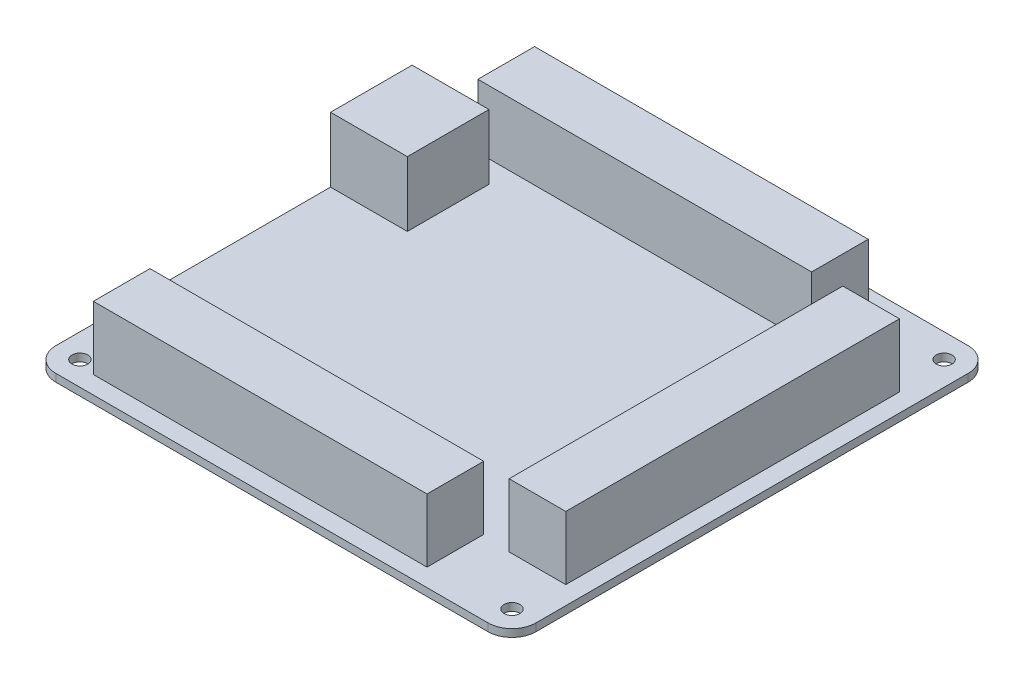
SolidWorks part; units mm, degrees
ref_plane "Front" through (0, 0, 0) normal (0, 0, 1) x (1, 0, 0)
ref_plane "Top" through (0, 0, 0) normal (0, 1, 0) x (1, 0, 0)
ref_plane "Right" through (0, 0, 0) normal (1, 0, 0) x (0, 0, -1)
sketch "Sketch1" plane through (0, 0, 0) normal (0, 1, 0) x (1, 0, 0)
  line L1 (-50, -50) -> (50, -50)
  line L2 (-50, -50) -> (-50, 50)
  line L3 (-50, 50) -> (50, 50)
  line L4 (50, -50) -> (50, 50)
  line L5 (-50, -50) -> (50, 50) construction
  line L6 (-50, 50) -> (50, -50) construction
  point P0 (0, 0)
  dimension "D1" = 100
  dimension "D2" = 100
extrude "Boss-Extrude1" add sketch "Sketch1" along normal blind 1.6
fillet "Fillet1" radius 5 4 edges at (-50, 0.8, -50) (50, 0.8, -50) (50, 0.8, 50) (-50, 0.8, 50)
hole_wizard "Ø3.3 (3.3) Diameter Hole1" positions "Sketch3" profile "Sketch2" hole size "Ø3.3" standard "ANSI Metric" end condition through all
sketch "Sketch3" plane through (0, 1.6, 0) normal (0, 1, 0) x (1, 0, 0)
  line L0 (-45, -50) -> (45, -50) construction
  line L1 (-50, 45) -> (-50, -45) construction
  line L2 (50, -45) -> (50, 45) construction
  line L3 (45, 50) -> (-45, 50) construction
  point P0 (45, -45)
  point P2 (-45, -45)
  point P4 (-45, 45)
  point P6 (45, 45)
  dimension "D1" = 5
  dimension "D2" = 5
  dimension "D3" = 5
  dimension "D4" = 5
sketch "Sketch2" plane through (45, 1.6, 45) normal (1, 0, 0) x (0, 0, 1)
  line L0 (0, 0) -> (0, 1.6)
  line L1 (0, 1.6) -> (1.65, 1.6)
  line L2 (1.65, 1.6) -> (1.65, 0)
  line L5 (1.65, 0) -> (0, 0)
  line L11 (0, -6.35) -> (0, 107.95) construction
  dimension "Thru Hole Dia." = 3.3
  dimension "Thru Hole Depth" = 1.6
sketch "Sketch4" plane through (0, 1.6, 0) normal (0, 1, 0) x (1, 0, 0)
  line L0 (-50, 29.2) -> (-34, 29.2)
  line L1 (-50, 45) -> (-50, -45) construction
  line L2 (-34, 29.2) -> (-34, 12.2)
  line L3 (-34, 12.2) -> (-50, 12.2)
  line L4 (45, 50) -> (-45, 50) construction
  line L8 (45, 50) -> (-45, 50)
  line L9 (-50, 45) -> (-50, -45)
  line L10 (-45, -50) -> (45, -50)
  line L11 (50, -45) -> (50, 45)
  line L13 (-50, 29.2) -> (-50, 12.2)
  arc A4 (-45, 50) -> (-50, 45) centre (-45, 45) ccw
  arc A5 (-50, -45) -> (-45, -50) centre (-45, -45) ccw
  arc A6 (45, -50) -> (50, -45) centre (45, -45) ccw
  arc A7 (50, 45) -> (45, 50) centre (45, 45) ccw
  dimension "D2" = 16
  dimension "D3" = 17
  dimension "D4" = 20.8
  dimension "D1" = 0
extrude "Boss-Extrude2" add sketch "Sketch4" along normal blind 13.5
sketch "Sketch5" plane through (0, 1.6, 0) normal (0, 1, 0) x (1, 0, 0)
  line L0 (-50, 45) -> (-50, 29.2) construction
  line L1 (-40.9, 45.6) -> (28.6, 45.6)
  line L2 (-40.9, 45.6) -> (-40.9, 33.8)
  line L3 (-40.9, 33.8) -> (28.6, 33.8)
  line L4 (28.6, 45.6) -> (28.6, 33.8)
  line L5 (34.4, 34.5) -> (46.2, 34.5)
  line L6 (34.4, 34.5) -> (34.4, -35)
  line L7 (34.4, -35) -> (46.2, -35)
  line L8 (46.2, 34.5) -> (46.2, -35)
  line L9 (-40.9, -34.5) -> (28.6, -34.5)
  line L10 (-40.9, -34.5) -> (-40.9, -46.3)
  line L11 (-40.9, -46.3) -> (28.6, -46.3)
  line L12 (28.6, -34.5) -> (28.6, -46.3)
  line L13 (45, 50) -> (-45, 50) construction
  line L14 (-50, 12.2) -> (-50, -45) construction
  line L15 (-45, -50) -> (45, -50) construction
  line L16 (50, -45) -> (50, 45) construction
  dimension "D1" = 9.1
  dimension "D2" = 69.5
  dimension "D3" = 4.4
  dimension "D4" = 11.8
  dimension "D5" = 69.5
  dimension "D6" = 11.8
  dimension "D7" = 69.5
  dimension "D8" = 11.8
  dimension "D9" = 9.1
  dimension "D10" = 3.7
  dimension "D11" = 15
  dimension "D12" = 3.8
extrude "Boss-Extrude3" add sketch "Sketch5" along normal blind 13.2
